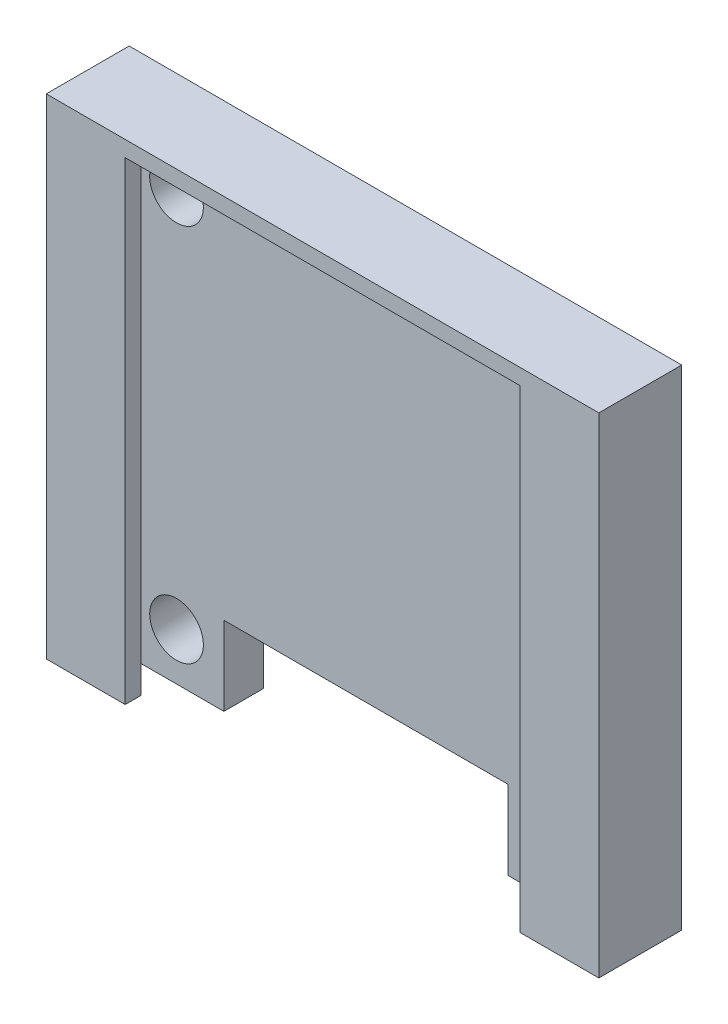
SolidWorks part; units mm, degrees
ref_plane "Front Plane" through (0, 0, 0) normal (0, 0, 1) x (1, 0, 0)
ref_plane "Top Plane" through (0, 0, 0) normal (0, 1, 0) x (1, 0, 0)
ref_plane "Right Plane" through (0, 0, 0) normal (1, 0, 0) x (0, 0, -1)
sketch "Sketch1" plane through (0, 0, 0) normal (0, 0, 1) x (1, 0, 0)
  line L0 (17.5, 30) -> (17.5, 0) construction
  line L1 (0, 0) -> (35, 0)
  line L2 (0, 0) -> (0, 30)
  line L3 (0, 30) -> (35, 30)
  line L4 (35, 0) -> (35, 30)
  line L5 (0, 15) -> (35, 15) construction
  circle A0 centre (5.5, 27) radius 1.7
  circle A1 centre (29.5, 27) radius 1.7
  circle A2 centre (29.5, 3) radius 1.7
  circle A3 centre (5.5, 3) radius 1.7
  dimension "D5" = 3.4
  dimension "D1" = 35
  dimension "D2" = 30
  dimension "D3" = 5.5
  dimension "D4" = 3
extrude "Boss-Extrude1" add sketch "Sketch1" along normal blind 2.5 contours L2 L3 L4 L1 | A0 | A3 | A2 | A1
sketch "Sketch3" plane through (0, 0, 2.5) normal (0, 0, 1) x (1, 0, 0)
  line L0 (0, 0) -> (35, 0) construction
  line L1 (8.5, 0) -> (26.5, 0)
  line L2 (8.5, 0) -> (8.5, 5)
  line L3 (8.5, 5) -> (26.5, 5)
  line L4 (26.5, 0) -> (26.5, 5)
  circle A0 centre (29.5, 3) radius 1.7 construction
  circle A1 centre (5.5, 3) radius 1.7 construction
  dimension "D2" = 3
  dimension "D1" = 5
  dimension "D3" = 3
extrude "Cut-Extrude1" cut sketch "Sketch3" against normal blind 5
sketch "Sketch4" plane through (0, 0, 2.5) normal (0, 0, 1) x (1, 0, 0)
  line L0 (0, 30) -> (35, 30) construction
  line L1 (0, 0) -> (2.5519, 0)
  line L2 (0, 0) -> (0, 30)
  line L3 (0, 30) -> (2.5519, 30)
  line L4 (2.5519, 0) -> (2.5519, 30)
  line L5 (17.5, 30) -> (17.5, 5) construction
  line L6 (26.5, 5) -> (8.5, 5) construction
  line L7 (35, 0) -> (32.4481, 0)
  line L8 (35, 0) -> (35, 30)
  line L9 (35, 30) -> (32.4481, 30)
  line L10 (32.4481, 0) -> (32.4481, 30)
extrude "Boss-Extrude2" add sketch "Sketch4" along normal blind 1.75
sketch "Sketch5" plane through (0, 0, 4.25) normal (0, 0, 1) x (1, 0, 0)
  line L0 (17.5, 30) -> (17.5, 5) construction
  line L1 (0, 30) -> (5, 30)
  line L2 (0, 30) -> (0, 0)
  line L3 (0, 0) -> (5, 0)
  line L4 (5, 30) -> (5, 0)
  line L5 (2.5519, 30) -> (32.4481, 30) construction
  line L6 (26.5, 5) -> (8.5, 5) construction
  line L7 (35, 0) -> (30, 0)
  line L8 (30, 30) -> (30, 0)
  line L9 (35, 30) -> (30, 30)
  line L10 (35, 30) -> (35, 0)
  line M5 (0, 30) -> (0, 0)
  line M6 (0, 0) -> (2.5519, 0)
  line M7 (2.5519, 0) -> (2.5519, 30)
  line M8 (2.5519, 30) -> (0, 30)
extrude "Boss-Extrude3" add sketch "Sketch5" along normal blind 1 contours L4 L1 L3 M7 | M8 M5 M6 M7 | L10 L9 L8 L7
sketch "Sketch6" plane through (0, 30, 0) normal (0, 1, 0) x (1, 0, 0)
  line L1 (0, 0) -> (35, 0)
  line L2 (0, 0) -> (0, -5.25)
  line L3 (0, -5.25) -> (35, -5.25)
  line L4 (35, 0) -> (35, -5.25)
extrude "Boss-Extrude4" add sketch "Sketch6" along normal blind 1
